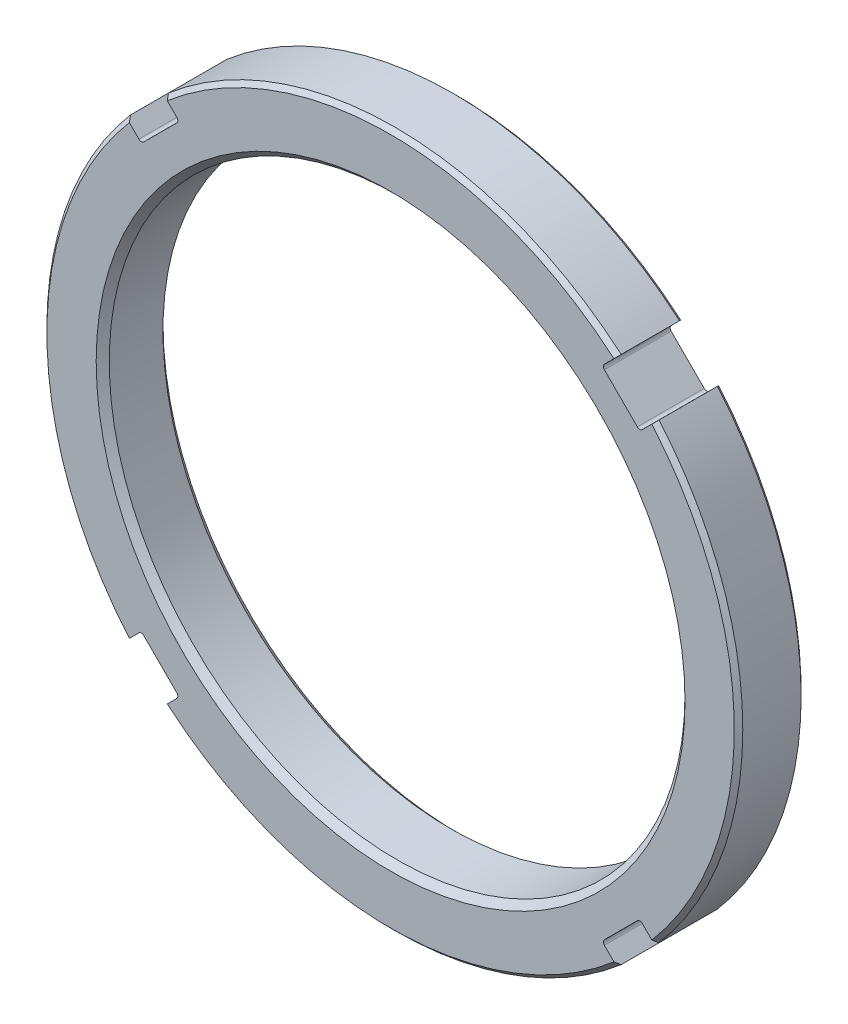
SolidWorks part; units mm, degrees
material "Alloy Steel"
ref_plane "Front Plane" through (0, 0, 0) normal (0, 0, 1) x (1, 0, 0)
ref_plane "Top Plane" through (0, 0, 0) normal (0, 1, 0) x (1, 0, 0)
ref_plane "Right Plane" through (0, 0, 0) normal (1, 0, 0) x (0, 0, -1)
sketch "Sketch1" plane through (0, 0, 0) normal (0, 0, 1) x (1, 0, 0)
  circle A0 centre (0, 0) radius 41.275
  circle A1 centre (0, 0) radius 34.1503
  dimension "D1" = 82.55
  dimension "D2" = 68.3006
extrude "Extrude1" add sketch "Sketch1" along normal blind 7.9248
chamfer "Chamfer1" distance 0.5032 angle 45 2 edges at (41.275, 0, 0) (41.275, 0, 7.9248)
chamfer "Chamfer2" distance 0.7747 angle 45 2 edges at (34.1503, 0, 0) (34.1503, 0, 7.9248)
sketch "Sketch2" plane through (0, 0, 7.9248) normal (0, 0, 1) x (1, 0, 0)
  line L0 (0, 0) -> (22.7176, 0) construction
  line L1 (0, 0) -> (15.6425, 15.6425) construction
  line L2 (26.8543, 31.3444) -> (25.0729, 29.563)
  line L3 (25.0729, 29.563) -> (29.563, 25.0729)
  line L4 (31.3444, 26.8543) -> (29.563, 25.0729)
  circle A0 centre (0, 0) radius 41.275 construction
  arc A1 (31.3444, 26.8543) -> (26.8543, 31.3444) centre (0, 0) ccw
  dimension "D3" = 2.6416
  dimension "D1" = 45
  dimension "D2" = 6.35
extrude "Cut-Extrude1" cut sketch "Sketch2" against normal through all
fillet "Fillet1" radius 0.4064 2 edges at (29.563, 25.0729, 3.9624) (25.0729, 29.563, 3.9624)
pattern_circular "CirPattern1" count 4 over 360 about axis through (0, 0, 0) along (0, 0, 1) of "Fillet1", "Cut-Extrude1"
